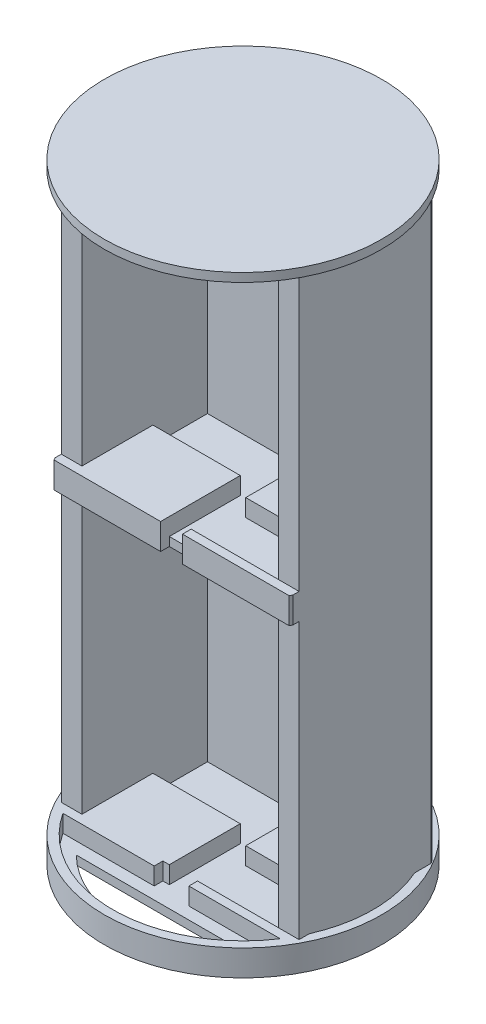
SolidWorks part; units mm, degrees
ref_plane "Front Plane" through (0, 0, 0) normal (0, 0, 1) x (1, 0, 0)
ref_plane "Top Plane" through (0, 0, 0) normal (0, 1, 0) x (1, 0, 0)
ref_plane "Right Plane" through (0, 0, 0) normal (1, 0, 0) x (0, 0, -1)
sketch "Sketch1" plane through (0, 0, 0) normal (0, 1, 0) x (1, 0, 0)
  circle A0 centre (0, 0) radius 50.8
  dimension "D1" = 101.6
extrude "Boss-Extrude1" add sketch "Sketch1" along normal blind 1
sketch "Sketch4" plane through (0, 1, 0) normal (0, 1, 0) x (1, 0, 0)
  line L0 (-36, 23) -> (36, -23) construction
  line L1 (-36, 23) -> (36, 23)
  line L2 (-36, 23) -> (-36, -23)
  line L3 (-36, -23) -> (36, -23)
  line L4 (36, 23) -> (36, -23)
  line L5 (-36, -23) -> (36, 23) construction
  line L6 (-36, 23) -> (-26, 23)
  line L7 (-36, 23) -> (-36, 18)
  line L8 (-36, 18) -> (-26, 18)
  line L9 (-26, 23) -> (-26, 18)
  line L10 (-26, 18) -> (4, 18)
  line L11 (-26, 18) -> (-26, 3)
  line L12 (-26, 3) -> (4, 3)
  line L13 (4, 18) -> (4, 3)
  line L14 (-39.175, 26.175) -> (39.175, 26.175)
  line L15 (36, -23) -> (26, -23)
  line L16 (36, -23) -> (36, -18)
  line L17 (36, -18) -> (26, -18)
  line L18 (26, -23) -> (26, -18)
  line L19 (26, -18) -> (-4, -18)
  line L20 (26, -18) -> (26, -3)
  line L21 (26, -3) -> (-4, -3)
  line L22 (-4, -18) -> (-4, -3)
  line L23 (4, 3) -> (-36, 3)
  line L24 (4, 3) -> (4, 23)
  line L25 (4, 23) -> (-36, 23)
  line L26 (-36, 3) -> (-36, 23)
  line L27 (-4, -3) -> (36, -3)
  line L28 (-4, -3) -> (-4, -23)
  line L29 (-4, -23) -> (36, -23)
  line L30 (36, -3) -> (36, -23)
  line L31 (39.175, 26.175) -> (39.175, -26.175)
  line L32 (-39.175, -26.175) -> (39.175, -26.175)
  line L33 (-39.175, 26.175) -> (-39.175, -26.175)
  line L35 (0, 0) -> (-6.35, 0)
  line L36 (0, 0) -> (0, 26.175)
  line L37 (0, 26.175) -> (-6.35, 26.175)
  line L38 (-6.35, 0) -> (-6.35, 26.175)
  line L39 (0, 0) -> (6.35, 0)
  line L40 (0, 0) -> (0, 26.175)
  line L41 (0, 26.175) -> (6.35, 26.175)
  line L42 (6.35, 0) -> (6.35, 26.175)
  line L43 (0, 0) -> (-6.35, 0)
  line L44 (0, 0) -> (0, -26.175)
  line L45 (0, -26.175) -> (-6.35, -26.175)
  line L46 (-6.35, 0) -> (-6.35, -26.175)
  line L47 (0, 0) -> (6.35, 0)
  line L48 (0, 0) -> (0, -26.175)
  line L49 (0, -26.175) -> (6.35, -26.175)
  line L50 (6.35, 0) -> (6.35, -26.175)
  circle A0 centre (0, 0) radius 50.8
  point P0 (0, 0)
  dimension "D1" = 72
  dimension "D2" = 46
  dimension "D3" = 10
  dimension "D4" = 5
  dimension "D5" = 15
  dimension "D6" = 30
  dimension "D7" = 10
  dimension "D8" = 5
  dimension "D9" = 30
  dimension "D10" = 15
  dimension "D12" = 6.35
  dimension "D13" = 6.35
  dimension "D14" = 6.35
  dimension "D15" = 6.35
  dimension "D11" = 3.175
extrude "Boss-Extrude2" add sketch "Sketch4" along normal blind 6.35 contours L46 L3 L2 L1 L38 L14 L33 L32 | L3 L50 L32 L31 L14 L42 L1 L4 | L46 L38 L12 L23 L2 L3 | L42 L50 L21 L27 L4 L1 | L38 L35 L36 L23 | L39 L42 L1 L24 L13 L23 L36 | L50 L39 L44 L27 | L35 L46 L3 L28 L22 L27 L44
sketch "Sketch6" plane through (0, 1, 0) normal (0, 1, 0) x (1, 0, 0)
  circle A0 centre (0, 0) radius 50.8
  circle A1 centre (0, 0) radius 47.625
  dimension "D2" = 101.6
  dimension "D1" = 3.175
extrude "Boss-Extrude3" add sketch "Sketch6" along normal blind 6.35
sketch "Sketch8" plane through (0, 1, 0) normal (0, 1, 0) x (1, 0, 0)
  line L0 (-36, 23) -> (-36, 26.175)
  line L1 (36, -23) -> (36, -26.175)
  line L2 (-36, 26.175) -> (-43.5374, 26.175)
  line L3 (-36, 26.175) -> (-36, -26.175)
  line L4 (-36, -26.175) -> (-43.5374, -26.175)
  line L5 (-43.5374, 26.175) -> (-43.5374, -26.175)
  line L6 (6.35, 26.175) -> (39.175, 26.175) construction
  line L7 (36, -26.175) -> (43.5374, -26.175)
  line L8 (36, -26.175) -> (36, 26.175)
  line L9 (36, 26.175) -> (43.5374, 26.175)
  line L10 (43.5374, -26.175) -> (43.5374, 26.175)
  line L11 (-36, 23) -> (-43.5374, 23)
  line L12 (-43.5374, 23) -> (43.5374, 23)
  line L13 (36, -23) -> (43.5374, -23)
  line L14 (43.5374, -23) -> (-43.5374, -23)
  line L20 (4, 3) -> (-36, 3)
  line L21 (-36, 3) -> (-36, 23)
  line L22 (-36, 23) -> (-6.35, 23)
  line L23 (-6.35, 23) -> (-6.35, 26.175)
  line L24 (-6.35, 26.175) -> (-39.175, 26.175)
  line L25 (-39.175, 26.175) -> (-39.175, -26.175)
  line L26 (-39.175, -26.175) -> (-6.35, -26.175)
  line L27 (-6.35, -26.175) -> (-6.35, -23)
  line L28 (-6.35, -23) -> (-4, -23)
  line L29 (-4, -23) -> (-4, -3)
  line L30 (-4, -3) -> (36, -3)
  line L31 (36, -3) -> (36, -23)
  line L32 (36, -23) -> (6.35, -23)
  line L33 (6.35, -23) -> (6.35, -26.175)
  line L34 (6.35, -26.175) -> (39.175, -26.175)
  line L35 (39.175, -26.175) -> (39.175, 26.175)
  line L36 (39.175, 26.175) -> (6.35, 26.175)
  line L37 (6.35, 26.175) -> (6.35, 23)
  line L38 (6.35, 23) -> (4, 23)
  line L39 (4, 23) -> (4, 3)
  line L40 (4, 3) -> (-36, 3)
  line L41 (-36, 3) -> (-36, 23)
  line L42 (-36, 23) -> (-6.35, 23)
  line L43 (-6.35, 23) -> (-6.35, 26.175)
  line L44 (-6.35, 26.175) -> (-39.175, 26.175)
  line L45 (-39.175, 26.175) -> (-39.175, -26.175)
  line L46 (-39.175, -26.175) -> (-6.35, -26.175)
  line L47 (-6.35, -26.175) -> (-6.35, -23)
  line L48 (-6.35, -23) -> (-4, -23)
  line L49 (-4, -23) -> (-4, -3)
  line L50 (-4, -3) -> (36, -3)
  line L51 (36, -3) -> (36, -23)
  line L52 (36, -23) -> (6.35, -23)
  line L53 (6.35, -23) -> (6.35, -26.175)
  line L54 (6.35, -26.175) -> (39.175, -26.175)
  line L55 (39.175, -26.175) -> (39.175, 26.175)
  line L56 (39.175, 26.175) -> (6.35, 26.175)
  line L57 (6.35, 26.175) -> (6.35, 23)
  line L58 (6.35, 23) -> (4, 23)
  line L59 (4, 23) -> (4, 3)
  circle A0 centre (0, 0) radius 47.625 construction
  circle A1 centre (0, 0) radius 47.625
  circle A2 centre (0, 0) radius 50.8 construction
  line M27 (39.175, 26.175) -> (39.175, -26.175)
  line M31 (36, -23) -> (36, -3)
  line M37 (-39.175, -26.175) -> (-39.175, 26.175)
  line M41 (-36, 23) -> (-36, 3)
  circle M42 centre (0, 0) radius 47.625
  dimension "D1" = 0
extrude "Boss-Extrude5" add sketch "Sketch8" along normal blind 107.28 contours L14 L11 L5 M37 M42 | L14 L3 L11 M41 M37 | L13 L12 L8 M31 M27 | L13 L10 L12 M27 M42 | L12 L10 M42 | L13 L10 M42 | L14 L5 M42 | L11 L5 M42
sketch "Sketch9" plane through (0, 7.35, 0) normal (0, 1, 0) x (1, 0, 0)
  line L0 (-43.5374, 23) -> (-49.3806, 23)
  line L1 (-49.3806, 23) -> (-49.3806, 26.175)
  line L2 (43.5374, 23) -> (49.0826, 23)
  line L3 (-43.5374, 23) -> (-43.5374, 25.3112)
  line L4 (-49.3806, 26.175) -> (49.0826, 26.175)
  line L5 (-49.3806, 26.175) -> (-49.3806, 23)
  line L6 (-49.3806, 23) -> (49.0826, 23)
  line L7 (49.0826, 26.175) -> (49.0826, 23)
  line L8 (43.5374, 23) -> (43.5374, 25.3112)
  circle A0 centre (0, 0) radius 50.8
  circle A1 centre (0, 0) radius 50.3604
  dimension "D1" = 3.175
extrude "Boss-Extrude10" add sketch "Sketch9" along normal up to surface and the other way up to surface
sketch "Sketch12" plane through (0, 108.28, 0) normal (0, 1, 0) x (1, 0, 0)
  line L0 (-36, -23) -> (36, -23)
  line L9 (36, 23) -> (36, -23)
  line L10 (36, -23) -> (43.5374, -23)
  line L11 (43.5374, -23) -> (43.5374, 25.3112)
  line L12 (43.0237, 26.175) -> (-43.0237, 26.175)
  line L13 (-43.5374, 25.3112) -> (-43.5374, -23)
  line L14 (-43.5374, -23) -> (-36, -23)
  line L15 (-36, -23) -> (-36, 23)
  line L16 (-36, 23) -> (36, 23)
  line L17 (36, 23) -> (36, -23)
  line L18 (36, -23) -> (43.5374, -23)
  line L19 (43.5374, -23) -> (43.5374, 25.3112)
  line L20 (43.0237, 26.175) -> (-43.0237, 26.175)
  line L21 (-43.5374, 25.3112) -> (-43.5374, -23)
  line L22 (-43.5374, -23) -> (-36, -23)
  line L23 (-36, -23) -> (-36, 23)
  line L24 (-36, 23) -> (36, 23)
  arc A2 (43.5374, 25.3112) -> (43.0237, 26.175) centre (0, 0) ccw
  arc A3 (-43.0237, 26.175) -> (-43.5374, 25.3112) centre (0, 0) ccw
  arc A4 (43.5374, 25.3112) -> (43.0237, 26.175) centre (0, 0) ccw
  arc A5 (-43.0237, 26.175) -> (-43.5374, 25.3112) centre (0, 0) ccw
  line M12 (36, 23) -> (36, -23)
  line M13 (36, -23) -> (43.5374, -23)
  line M14 (43.5374, -23) -> (43.5374, 25.3112)
  arc M15 (43.5374, 25.3112) -> (43.0237, 26.175) centre (0, 0) ccw
  line M16 (43.0237, 26.175) -> (-43.0237, 26.175)
  arc M17 (-43.0237, 26.175) -> (-43.5374, 25.3112) centre (0, 0) ccw
  line M18 (-43.5374, 25.3112) -> (-43.5374, -23)
  line M19 (-43.5374, -23) -> (-36, -23)
  line M20 (-36, -23) -> (-36, 23)
  line M21 (-36, 23) -> (36, 23)
  dimension "D1" = 0
extrude "Boss-Extrude13" add sketch "Sketch12" along normal blind 3.175 contours M21 M12 M13 M14 M15 M16 M17 M18 M19 M20 | L0 M20 M12 M21
sketch "Sketch13" plane through (0, 111.455, 0) normal (0, 1, 0) x (1, 0, 0)
  line L0 (39.175, -26.175) -> (39.175, -23) construction
  line L1 (39.175, -23) -> (36, -23) construction
  line L2 (36, -23) -> (6.35, -23) construction
  line L3 (6.35, -23) -> (6.35, -26.175) construction
  line L4 (6.35, -26.175) -> (39.175, -26.175) construction
  line L5 (4, 3) -> (4, 23) construction
  line L6 (4, 23) -> (-36, 23) construction
  line L7 (-36, 23) -> (-36, 3) construction
  line L8 (-36, 3) -> (4, 3) construction
  line L9 (-39.175, -23) -> (-41.703, -23) construction
  line L10 (41.703, -23) -> (39.175, -23) construction
  line L11 (39.175, -23) -> (39.175, -26.175) construction
  line L12 (39.175, -26.175) -> (6.35, -26.175) construction
  line L13 (6.35, -26.175) -> (6.35, -23) construction
  line L14 (6.35, -23) -> (36, -23) construction
  line L15 (36, -23) -> (36, -3) construction
  line L16 (36, -3) -> (-4, -3) construction
  line L17 (-4, -3) -> (-4, -23) construction
  line L18 (-4, -23) -> (-6.35, -23) construction
  line L19 (-6.35, -23) -> (-6.35, -26.175) construction
  line L20 (-6.35, -26.175) -> (-39.175, -26.175) construction
  line L21 (-39.175, -26.175) -> (-39.175, -23) construction
  line L22 (36, -3) -> (36, 23) construction
  line L23 (36, 23) -> (4, 23) construction
  line L24 (4, 23) -> (4, 3) construction
  line L25 (4, 3) -> (-36, 3) construction
  line L26 (-36, 3) -> (-36, -23) construction
  line L27 (-36, -23) -> (-39.175, -23) construction
  line L28 (-39.175, -23) -> (-39.175, -26.175) construction
  line L29 (-39.175, -26.175) -> (-6.35, -26.175) construction
  line L30 (-6.35, -26.175) -> (-6.35, -23) construction
  line L31 (-6.35, -23) -> (-4, -23) construction
  line L32 (-4, -23) -> (-4, -3) construction
  line L33 (-4, -3) -> (36, -3) construction
  line L34 (-43.5374, 25.3112) -> (-43.5374, -23) construction
  line L35 (-43.5374, -23) -> (43.5374, -23) construction
  line L36 (43.5374, -23) -> (43.5374, 25.3112) construction
  line L37 (43.0237, 26.175) -> (-43.0237, 26.175) construction
  line L38 (39.175, -26.175) -> (39.175, -23)
  line L39 (39.175, -23) -> (36, -23)
  line L40 (36, -23) -> (6.35, -23)
  line L41 (6.35, -23) -> (6.35, -26.175)
  line L42 (6.35, -26.175) -> (39.175, -26.175)
  line L43 (4, 3) -> (4, 23)
  line L44 (4, 23) -> (-36, 23)
  line L45 (-36, 23) -> (-36, 3)
  line L46 (-36, 3) -> (4, 3)
  line L47 (-39.175, -23) -> (-41.703, -23)
  line L48 (41.703, -23) -> (39.175, -23)
  line L49 (39.175, -23) -> (39.175, -26.175)
  line L50 (39.175, -26.175) -> (6.35, -26.175)
  line L51 (6.35, -26.175) -> (6.35, -23)
  line L52 (6.35, -23) -> (36, -23)
  line L53 (36, -23) -> (36, -3)
  line L54 (36, -3) -> (-4, -3)
  line L55 (-4, -3) -> (-4, -23)
  line L56 (-4, -23) -> (-6.35, -23)
  line L57 (-6.35, -23) -> (-6.35, -26.175)
  line L58 (-6.35, -26.175) -> (-39.175, -26.175)
  line L59 (-39.175, -26.175) -> (-39.175, -23)
  line L60 (36, -3) -> (36, 23)
  line L61 (36, 23) -> (4, 23)
  line L62 (4, 23) -> (4, 3)
  line L63 (4, 3) -> (-36, 3)
  line L64 (-36, 3) -> (-36, -23)
  line L65 (-36, -23) -> (-39.175, -23)
  line L66 (-39.175, -23) -> (-39.175, -26.175)
  line L67 (-39.175, -26.175) -> (-6.35, -26.175)
  line L68 (-6.35, -26.175) -> (-6.35, -23)
  line L69 (-6.35, -23) -> (-4, -23)
  line L70 (-4, -23) -> (-4, -3)
  line L71 (-4, -3) -> (36, -3)
  line L72 (-43.5374, 25.3112) -> (-43.5374, -23)
  line L73 (-43.5374, -23) -> (43.5374, -23)
  line L74 (43.5374, -23) -> (43.5374, 25.3112)
  line L75 (43.0237, 26.175) -> (-43.0237, 26.175)
  line L77 (4, 23) -> (-4, 23)
  line L78 (4, 23) -> (4, 26.175)
  line L79 (4, 26.175) -> (-4, 26.175)
  line L80 (-4, 23) -> (-4, 26.175)
  arc A0 (-41.703, -23) -> (41.703, -23) centre (0, 0) ccw construction
  arc A1 (43.5374, 25.3112) -> (43.0237, 26.175) centre (0, 0) ccw construction
  arc A2 (-43.0237, 26.175) -> (-43.5374, 25.3112) centre (0, 0) ccw construction
  arc A3 (-41.703, -23) -> (41.703, -23) centre (0, 0) ccw
  arc A4 (43.5374, 25.3112) -> (43.0237, 26.175) centre (0, 0) ccw
  arc A5 (-43.0237, 26.175) -> (-43.5374, 25.3112) centre (0, 0) ccw
  line M1 (-43.5374, 25.3112) -> (-43.5374, -23)
  line M2 (-43.5374, -23) -> (43.5374, -23)
  line M3 (43.5374, -23) -> (43.5374, 25.3112)
  arc M4 (43.5374, 25.3112) -> (43.0237, 26.175) centre (0, 0) ccw
  line M5 (43.0237, 26.175) -> (-43.0237, 26.175)
  arc M6 (-43.0237, 26.175) -> (-43.5374, 25.3112) centre (0, 0) ccw
extrude "Boss-Extrude14" add sketch "Sketch13" along normal blind 6.35 contours L46 L64 L55 L54 L60 L61 L43 M2 | L78 L61 L60 L53 M2 M3 M4 M5 | L44 L80 L64 L45 M5 M6 M1 M2
sketch "Sketch15" plane through (0, 1, 0) normal (0, 1, 0) x (1, 0, 0)
  line L0 (-39.175, -26.175) -> (-39.7871, -26.175)
  line L1 (39.175, -26.175) -> (39.7871, -26.175)
  line L13 (-39.175, -23) -> (-41.703, -23)
  line L14 (41.703, -23) -> (39.175, -23)
  line L15 (39.175, -23) -> (39.175, -26.175)
  line L16 (39.175, -26.175) -> (6.35, -26.175)
  line L17 (6.35, -26.175) -> (6.35, -23)
  line L18 (6.35, -23) -> (36, -23)
  line L19 (36, -23) -> (36, -3)
  line L20 (36, -3) -> (-4, -3)
  line L21 (-4, -3) -> (-4, -23)
  line L22 (-4, -23) -> (-6.35, -23)
  line L23 (-6.35, -23) -> (-6.35, -26.175)
  line L24 (-6.35, -26.175) -> (-39.175, -26.175)
  line L25 (-39.175, -26.175) -> (-39.175, -23)
  line L26 (-39.175, -23) -> (-41.703, -23)
  line L27 (41.703, -23) -> (39.175, -23)
  line L28 (39.175, -23) -> (39.175, -26.175)
  line L29 (39.175, -26.175) -> (6.35, -26.175)
  line L30 (6.35, -26.175) -> (6.35, -23)
  line L31 (6.35, -23) -> (36, -23)
  line L32 (36, -23) -> (36, -3)
  line L33 (36, -3) -> (-4, -3)
  line L34 (-4, -3) -> (-4, -23)
  line L35 (-4, -23) -> (-6.35, -23)
  line L36 (-6.35, -23) -> (-6.35, -26.175)
  line L37 (-6.35, -26.175) -> (-39.175, -26.175)
  line L38 (-39.175, -26.175) -> (-39.175, -23)
  arc A1 (-41.703, -23) -> (41.703, -23) centre (0, 0) ccw
  arc A2 (-41.703, -23) -> (41.703, -23) centre (0, 0) ccw
  arc A3 (-43.0237, 26.175) -> (-43.5374, 25.3112) centre (0, 0) ccw construction
  arc A4 (-43.0237, 26.175) -> (-43.5374, 25.3112) centre (0, 0) ccw
  circle A5 centre (0, 0) radius 50.3604
  line M15 (-39.175, -23) -> (-41.703, -23)
  arc M16 (-41.703, -23) -> (41.703, -23) centre (0, 0) ccw
  line M17 (41.703, -23) -> (39.175, -23)
  line M18 (39.175, -23) -> (39.175, -26.175)
  line M28 (-39.175, -26.175) -> (-39.175, -23)
  dimension "D1" = 0
extrude "Boss-Extrude16" add sketch "Sketch15" along normal up to surface (6.35 mm away) contours L1 M18 M16 M17 | L0 M28 M15 M16 up to face at (25.41, 7.35, 24.27)
sketch "Sketch16" plane through (0, 117.805, 0) normal (0, 1, 0) x (1, 0, 0)
  line L0 (-43.5374, -23) -> (-60.997, -23)
  line L1 (43.5374, -23) -> (67.6977, -23)
  line L2 (67.6977, -23) -> (67.6977, -26.175)
  line L3 (-43.5374, -23) -> (-43.5374, -25.3112)
  line L4 (67.6977, -26.175) -> (-60.997, -26.175)
  line L5 (67.6977, -26.175) -> (67.6977, -23)
  line L6 (67.6977, -23) -> (-60.997, -23)
  line L7 (-60.997, -26.175) -> (-60.997, -23)
  line L8 (4, 26.175) -> (-4, 26.175)
  line L9 (4, 26.175) -> (4, -26.175)
  line L10 (4, -26.175) -> (-4, -26.175)
  line L11 (-4, 26.175) -> (-4, -26.175)
  line L12 (43.5374, -23) -> (43.5374, -25.3112)
  line L14 (4, 3) -> (-36, 3)
  line L15 (-36, 3) -> (-36, 23)
  line L16 (-36, 23) -> (-4, 23)
  line L17 (-4, 23) -> (-4, 26.175)
  line L18 (-4, 26.175) -> (-43.0237, 26.175)
  line L19 (-43.5374, 25.3112) -> (-43.5374, -23)
  line L20 (-43.5374, -23) -> (-4, -23)
  line L21 (-4, -23) -> (-4, -3)
  line L22 (-4, -3) -> (36, -3)
  line L23 (36, -3) -> (36, -23)
  line L24 (36, -23) -> (43.5374, -23)
  line L25 (43.5374, -23) -> (43.5374, 25.3112)
  line L26 (43.0237, 26.175) -> (4, 26.175)
  line L27 (4, 26.175) -> (4, 3)
  line L28 (4, 3) -> (-36, 3)
  line L29 (-36, 3) -> (-36, 23)
  line L30 (-36, 23) -> (-4, 23)
  line L31 (-4, 23) -> (-4, 26.175)
  line L32 (-4, 26.175) -> (-43.0237, 26.175)
  line L33 (-43.5374, 25.3112) -> (-43.5374, -23)
  line L34 (-43.5374, -23) -> (-4, -23)
  line L35 (-4, -23) -> (-4, -3)
  line L36 (-4, -3) -> (36, -3)
  line L37 (36, -3) -> (36, -23)
  line L38 (36, -23) -> (43.5374, -23)
  line L39 (43.5374, -23) -> (43.5374, 25.3112)
  line L40 (43.0237, 26.175) -> (4, 26.175)
  line L41 (4, 26.175) -> (4, 3)
  circle A0 centre (0, 0) radius 50.3604
  arc A2 (-43.0237, 26.175) -> (-43.5374, 25.3112) centre (0, 0) ccw
  arc A3 (43.5374, 25.3112) -> (43.0237, 26.175) centre (0, 0) ccw
  arc A4 (-43.0237, 26.175) -> (-43.5374, 25.3112) centre (0, 0) ccw
  arc A5 (43.5374, 25.3112) -> (43.0237, 26.175) centre (0, 0) ccw
  line M25 (-43.5374, -23) -> (-4, -23)
  line M29 (36, -23) -> (43.5374, -23)
  dimension "D2" = 3.175
  dimension "D1" = 0
extrude "Boss-Extrude17" add sketch "Sketch16" against normal up to surface (9.525 mm away) contours L0 A0 L4 L11 M25 | L4 A0 L1 L6 L9 M29
sketch "Sketch17" plane through (0, 117.805, 0) normal (0, 1, 0) x (1, 0, 0)
  line L0 (43.5374, 19.3037) -> (43.5374, -19.3037) construction
  line L1 (-39.7871, 26.175) -> (39.7871, 26.175) construction
  line L2 (-43.5374, -19.3037) -> (-43.5374, 19.3037) construction
  line L3 (-6.35, -26.175) -> (-39.7871, -26.175) construction
  line L4 (39.7871, -26.175) -> (6.35, -26.175) construction
  line L5 (6.35, -26.175) -> (6.35, -23) construction
  line L6 (6.35, -23) -> (36, -23) construction
  line L7 (36, -23) -> (36, -3) construction
  line L8 (36, -3) -> (-4, -3) construction
  line L9 (-4, -3) -> (-4, -23) construction
  line L10 (-4, -23) -> (-6.35, -23) construction
  line L11 (-6.35, -23) -> (-6.35, -26.175) construction
  line L12 (4, 3) -> (4, 23) construction
  line L13 (4, 23) -> (-36, 23) construction
  line L14 (-36, 23) -> (-36, 3) construction
  line L15 (-36, 3) -> (4, 3) construction
  line L16 (43.5374, 19.3037) -> (43.5374, -19.3037)
  line L17 (-39.7871, 26.175) -> (39.7871, 26.175)
  line L18 (-43.5374, -19.3037) -> (-43.5374, 19.3037)
  line L19 (-6.35, -26.175) -> (-39.7871, -26.175)
  line L20 (39.7871, -26.175) -> (6.35, -26.175)
  line L21 (6.35, -26.175) -> (6.35, -23)
  line L22 (6.35, -23) -> (36, -23)
  line L23 (36, -23) -> (36, -3)
  line L24 (36, -3) -> (-4, -3)
  line L25 (-4, -3) -> (-4, -23)
  line L26 (-4, -23) -> (-6.35, -23)
  line L27 (-6.35, -23) -> (-6.35, -26.175)
  line L28 (4, 3) -> (4, 23)
  line L29 (4, 23) -> (-36, 23)
  line L30 (-36, 23) -> (-36, 3)
  line L31 (-36, 3) -> (4, 3)
  line L32 (-36, -23) -> (-43.5374, -23)
  line L33 (36, -23) -> (-36, -23)
  line L34 (36, -23) -> (36, 23)
  line L35 (36, 23) -> (-36, 23)
  line L36 (-36, -23) -> (-36, 23)
  line L37 (-43.5374, -23) -> (43.5374, -23)
  line L48 (4, 3) -> (-36, 3)
  line L49 (-36, 3) -> (-36, 23)
  line L50 (-36, 23) -> (-4, 23)
  line L51 (-4, 23) -> (-4, 26.175)
  line L52 (-4, 26.175) -> (-43.0237, 26.175)
  line L53 (-43.5374, 25.3112) -> (-43.5374, -25.3112)
  line L54 (-43.0237, -26.175) -> (-4, -26.175)
  line L55 (-4, -26.175) -> (-4, -3)
  line L56 (-4, -3) -> (36, -3)
  line L57 (36, -3) -> (36, -23)
  line L58 (36, -23) -> (4, -23)
  line L59 (4, -23) -> (4, -26.175)
  line L60 (4, -26.175) -> (43.0237, -26.175)
  line L61 (43.5374, -25.3112) -> (43.5374, 25.3112)
  line L62 (43.0237, 26.175) -> (4, 26.175)
  line L63 (4, 26.175) -> (4, 3)
  line L64 (4, 3) -> (-36, 3)
  line L65 (-36, 3) -> (-36, 23)
  line L66 (-36, 23) -> (-4, 23)
  line L67 (-4, 23) -> (-4, 26.175)
  line L68 (-4, 26.175) -> (-43.0237, 26.175)
  line L69 (-43.5374, 25.3112) -> (-43.5374, -25.3112)
  line L70 (-43.0237, -26.175) -> (-4, -26.175)
  line L71 (-4, -26.175) -> (-4, -3)
  line L72 (-4, -3) -> (36, -3)
  line L73 (36, -3) -> (36, -23)
  line L74 (36, -23) -> (4, -23)
  line L75 (4, -23) -> (4, -26.175)
  line L76 (4, -26.175) -> (43.0237, -26.175)
  line L77 (43.5374, -25.3112) -> (43.5374, 25.3112)
  line L78 (43.0237, 26.175) -> (4, 26.175)
  line L79 (4, 26.175) -> (4, 3)
  arc A0 (43.5374, -19.3037) -> (43.5374, 19.3037) centre (0, 0) ccw construction
  arc A1 (39.7871, 26.175) -> (-39.7871, 26.175) centre (0, 0) ccw construction
  arc A2 (-43.5374, 19.3037) -> (-43.5374, -19.3037) centre (0, 0) ccw construction
  arc A3 (-39.7871, -26.175) -> (39.7871, -26.175) centre (0, 0) ccw construction
  circle A4 centre (0, 0) radius 50.8 construction
  arc A5 (43.5374, -19.3037) -> (43.5374, 19.3037) centre (0, 0) ccw
  arc A6 (39.7871, 26.175) -> (-39.7871, 26.175) centre (0, 0) ccw
  arc A7 (-43.5374, 19.3037) -> (-43.5374, -19.3037) centre (0, 0) ccw
  arc A8 (-39.7871, -26.175) -> (39.7871, -26.175) centre (0, 0) ccw
  circle A9 centre (0, 0) radius 50.8
  arc A14 (-43.0237, 26.175) -> (-43.5374, 25.3112) centre (0, 0) ccw
  arc A15 (-43.5374, -25.3112) -> (-43.0237, -26.175) centre (0, 0) ccw
  arc A16 (43.0237, -26.175) -> (43.5374, -25.3112) centre (0, 0) ccw
  arc A17 (43.5374, 25.3112) -> (43.0237, 26.175) centre (0, 0) ccw
  arc A18 (-43.0237, 26.175) -> (-43.5374, 25.3112) centre (0, 0) ccw
  arc A19 (-43.5374, -25.3112) -> (-43.0237, -26.175) centre (0, 0) ccw
  arc A20 (43.0237, -26.175) -> (43.5374, -25.3112) centre (0, 0) ccw
  arc A21 (43.5374, 25.3112) -> (43.0237, 26.175) centre (0, 0) ccw
  line M22 (-36, 3) -> (-36, 23)
  line M23 (-36, 23) -> (-4, 23)
  line M24 (-4, 23) -> (-4, 26.175)
  line M25 (-4, 26.175) -> (-43.0237, 26.175)
  arc M26 (-43.0237, 26.175) -> (-43.5374, 25.3112) centre (0, 0) ccw
  line M27 (-43.5374, 25.3112) -> (-43.5374, -25.3112)
  line M32 (36, -3) -> (36, -23)
  line M37 (43.5374, -25.3112) -> (43.5374, 25.3112)
  arc M38 (43.5374, 25.3112) -> (43.0237, 26.175) centre (0, 0) ccw
  line M39 (43.0237, 26.175) -> (4, 26.175)
  line M40 (4, 26.175) -> (4, 3)
  dimension "D1" = 0
extrude "Boss-Extrude18" add sketch "Sketch17" along normal blind 101 contours L32 L36 M22 M23 M24 M25 M26 M27 | L37 L35 L34 M32 M37 M38 M39 M40 | L29 L17 M40 M24
sketch "Sketch18" plane through (0, 0, -26.175) normal (0, 0, -1) x (-1, 0, 0)
  line L1 (-4, 117.805) -> (4, 117.805)
  line L2 (-4, 117.805) -> (-4, 111.455)
  line L3 (-4, 111.455) -> (4, 111.455)
  line L4 (4, 117.805) -> (4, 111.455)
extrude "Boss-Extrude19" add sketch "Sketch18" against normal up to surface (3.175 mm away) up to face at (-0.5714, 144.8479, -23)
sketch "Sketch19" plane through (0, 117.805, 0) normal (0, 1, 0) x (1, 0, 0)
  line L1 (-4, -3) -> (4, -3)
  line L2 (-4, -3) -> (-4, 3)
  line L3 (-4, 3) -> (4, 3)
  line L4 (4, -3) -> (4, 3)
extrude "Cut-Extrude1" cut sketch "Sketch19" against normal up to surface (6.35 mm away) contours L2 L3 L4 L1 up to face at (-16, 111.455, -13)
sketch "Sketch20" plane through (0, 7.35, 0) normal (0, 1, 0) x (1, 0, 0)
  line L1 (-4, -3) -> (4, -3)
  line L2 (-4, -3) -> (-4, 3)
  line L3 (-4, 3) -> (4, 3)
  line L4 (4, -3) -> (4, 3)
extrude "Cut-Extrude2" cut sketch "Sketch20" against normal up to surface (6.35 mm away) up to face at (6.4, 1, 22.415)
sketch "Sketch21" plane through (0, 218.805, 0) normal (0, 1, 0) x (1, 0, 0)
  line L0 (-43.0237, -26.175) -> (43.0237, -26.175)
  line L1 (43.5374, -23) -> (43.5374, -25.3112)
  line L2 (-43.5374, -23) -> (-43.5374, -25.3112)
  line L8 (-43.5374, -23) -> (-36, -23)
  line L9 (-36, -23) -> (-36, 23)
  line L10 (-36, 23) -> (36, 23)
  line L11 (36, 23) -> (36, -23)
  line L12 (36, -23) -> (43.5374, -23)
  line L13 (43.5374, -23) -> (43.5374, 25.3112)
  line L14 (43.0237, 26.175) -> (-43.0237, 26.175)
  line L15 (-43.5374, 25.3112) -> (-43.5374, -23)
  line L16 (-43.5374, -23) -> (-36, -23)
  line L17 (-36, -23) -> (-36, 23)
  line L18 (-36, 23) -> (36, 23)
  line L19 (36, 23) -> (36, -23)
  line L20 (36, -23) -> (43.5374, -23)
  line L21 (43.5374, -23) -> (43.5374, 25.3112)
  line L22 (43.0237, 26.175) -> (-43.0237, 26.175)
  line L23 (-43.5374, 25.3112) -> (-43.5374, -23)
  circle A0 centre (0, 0) radius 50.3604
  arc A2 (43.5374, 25.3112) -> (43.0237, 26.175) centre (0, 0) ccw
  arc A3 (-43.0237, 26.175) -> (-43.5374, 25.3112) centre (0, 0) ccw
  arc A4 (43.5374, 25.3112) -> (43.0237, 26.175) centre (0, 0) ccw
  arc A5 (-43.0237, 26.175) -> (-43.5374, 25.3112) centre (0, 0) ccw
  line M11 (-43.5374, -23) -> (-36, -23)
  line M12 (-36, -23) -> (-36, 23)
  line M13 (-36, 23) -> (36, 23)
  line M14 (36, 23) -> (36, -23)
  line M15 (36, -23) -> (43.5374, -23)
  line M16 (43.5374, -23) -> (43.5374, 25.3112)
  arc M17 (43.5374, 25.3112) -> (43.0237, 26.175) centre (0, 0) ccw
  line M18 (43.0237, 26.175) -> (-43.0237, 26.175)
  arc M19 (-43.0237, 26.175) -> (-43.5374, 25.3112) centre (0, 0) ccw
  line M20 (-43.5374, 25.3112) -> (-43.5374, -23)
  dimension "D1" = 0
extrude "Boss-Extrude21" add sketch "Sketch21" along normal blind 6 contours M20 M11 M12 M13 M14 M15 M16 M17 M18 M19 | L0 A0 L1 L2 M15 M14 M13 M12 M11
sketch "Sketch23" plane through (0, 1, 0) normal (0, 1, 0) x (1, 0, 0)
  line L0 (4, -3) -> (4, 23) construction
  line L1 (4, 23) -> (-36, 23) construction
  line L2 (-36, 23) -> (-36, 3) construction
  line L3 (-36, 3) -> (-4, 3) construction
  line L4 (-4, 3) -> (-4, -23) construction
  line L5 (-4, -23) -> (-6.35, -23) construction
  line L6 (-6.35, -23) -> (-6.35, -26.175) construction
  line L7 (-6.35, -26.175) -> (-39.7871, -26.175) construction
  line L8 (39.7871, -26.175) -> (6.35, -26.175) construction
  line L9 (6.35, -26.175) -> (6.35, -23) construction
  line L10 (6.35, -23) -> (36, -23) construction
  line L11 (36, -23) -> (36, -3) construction
  line L12 (36, -3) -> (4, -3) construction
  line L13 (-39.7871, 26.175) -> (39.7871, 26.175) construction
  line L14 (4, -3) -> (4, 23)
  line L15 (4, 23) -> (-36, 23)
  line L16 (-36, 23) -> (-36, 3)
  line L17 (-36, 3) -> (-4, 3)
  line L18 (-4, 3) -> (-4, -23)
  line L19 (-4, -23) -> (-6.35, -23)
  line L20 (-6.35, -23) -> (-6.35, -26.175)
  line L21 (-6.35, -26.175) -> (-39.7871, -26.175)
  line L22 (39.7871, -26.175) -> (6.35, -26.175)
  line L23 (6.35, -26.175) -> (6.35, -23)
  line L24 (6.35, -23) -> (36, -23)
  line L25 (36, -23) -> (36, -3)
  line L26 (36, -3) -> (4, -3)
  line L27 (-39.7871, 26.175) -> (39.7871, 26.175)
  line L28 (-6.35, -26.175) -> (6.35, -26.175)
  line L29 (-30.4455, 30.62) -> (30.4455, 30.62)
  line L30 (30.4455, -30.62) -> (6.35, -30.62)
  line L31 (-6.35, -30.62) -> (6.35, -30.62)
  line L32 (-6.35, -30.62) -> (-30.4455, -30.62)
  arc A0 (-39.7871, -26.175) -> (39.7871, -26.175) centre (0, 0) ccw construction
  arc A1 (39.7871, 26.175) -> (-39.7871, 26.175) centre (0, 0) ccw construction
  arc A2 (-39.7871, -26.175) -> (39.7871, -26.175) centre (0, 0) ccw
  arc A3 (39.7871, 26.175) -> (-39.7871, 26.175) centre (0, 0) ccw
  arc A4 (30.4455, 30.62) -> (-30.4455, 30.62) centre (0, 0) ccw
  arc A5 (-30.4455, -30.62) -> (30.4455, -30.62) centre (0, 0) ccw
  dimension "D1" = 4.445
extrude "Cut-Extrude3" cut sketch "Sketch23" against normal through all contours L32 A5 L30 L31 | L29 A4
sketch "Sketch24" plane through (0, 224.805, 0) normal (0, 1, 0) x (1, 0, 0)
  circle A0 centre (0, 0) radius 50.8
extrude "Boss-Extrude22" add sketch "Sketch24" against normal blind 6.35
sketch "Sketch25" plane through (0, 224.805, 0) normal (0, 1, 0) x (1, 0, 0)
  circle A1 centre (0, 0) radius 50.8
  circle A2 centre (0, 0) radius 50.8
  dimension "D1" = 0
extrude "Cut-Extrude4" cut sketch "Sketch25" against normal blind 3.175
sketch "Sketch26" plane through (0, 0, 0) normal (0, -1, 0) x (1, 0, 0)
  line L0 (-30.4455, -30.62) -> (30.4455, -30.62) construction
  line L1 (30.4455, 30.62) -> (-30.4455, 30.62) construction
  line L2 (-30.4455, -30.62) -> (30.4455, -30.62)
  line L3 (30.4455, 30.62) -> (-30.4455, 30.62)
  arc A0 (-30.4455, -30.62) -> (30.4455, -30.62) centre (0, 0) ccw construction
  circle A1 centre (0, 0) radius 50.8
  circle A2 centre (0, 0) radius 50.8
  arc A3 (30.4455, 30.62) -> (-30.4455, 30.62) centre (0, 0) ccw construction
  arc A4 (-30.4455, -30.62) -> (30.4455, -30.62) centre (0, 0) ccw
  arc A5 (30.4455, 30.62) -> (-30.4455, 30.62) centre (0, 0) ccw
  circle A6 centre (0, 0) radius 50.8
  arc M2 (-30.4455, 30.62) -> (30.4455, 30.62) centre (0, 0) cw
  line M3 (30.4455, 30.62) -> (-30.4455, 30.62)
  arc M4 (30.4455, -30.62) -> (-30.4455, -30.62) centre (0, 0) cw
  line M5 (-30.4455, -30.62) -> (30.4455, -30.62)
  circle M6 centre (0, 0) radius 50.8
  dimension "D1" = 0
extrude "Boss-Extrude23" add sketch "Sketch26" along normal blind 5.35 contours M6 M5 M4 M3 M2
sketch "Sketch28" plane through (0, -5.35, 0) normal (0, -1, 0) x (1, 0, 0)
  circle A0 centre (0, 0) radius 60.9686
extrude "Cut-Extrude5" cut sketch "Sketch28" against normal blind 3.175
